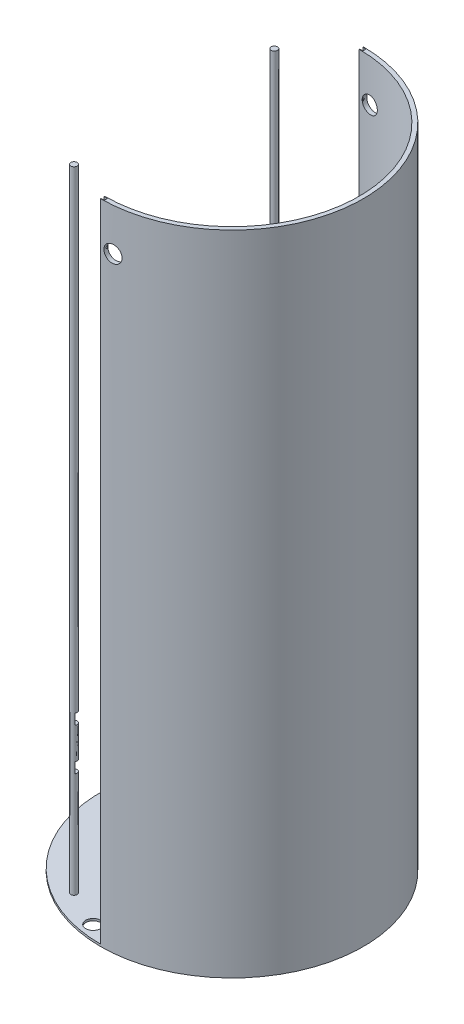
SolidWorks part; units mm, degrees
material "ABS"
ref_plane "Front Plane" through (0, 0, 0) normal (0, 0, 1) x (1, 0, 0)
ref_plane "Top Plane" through (0, 0, 0) normal (0, 1, 0) x (1, 0, 0)
ref_plane "Right Plane" through (0, 0, 0) normal (1, 0, 0) x (0, 0, -1)
sketch "Sketch2" plane through (0, 0, 0) normal (0, 1, 0) x (1, 0, 0)
  circle A0 centre (0, 0) radius 62.5
  circle A1 centre (0, 10) radius 0.75
  circle A2 centre (8.6603, -5) radius 0.75
  circle A3 centre (-8.6603, -5) radius 0.75
  point P12 (0, 0)
  dimension "D1" = 125
  dimension "D2" = 1.5
  dimension "D3" = 10
  dimension "D4" = 3
extrude "Boss-Extrude1" add sketch "Sketch2" along normal blind 1
sketch "Sketch3" plane through (0, 1, 0) normal (0, 1, 0) x (1, 0, 0)
  circle A0 centre (55, 0) radius 1.5
  dimension "D2" = 3
  dimension "D1" = 55
extrude "Boss-Extrude2" add sketch "Sketch3" along normal blind 300
ref_plane "Plane1" through (55, 0, 0) normal (1, 0, 0) x (0, 0, -1)
sketch "Sketch5" plane through (55, 0, 0) normal (1, 0, 0) x (0, 0, -1)
  line L0 (1.5, 1) -> (1.5, 301) construction
  line L1 (1.5, 56) -> (-1.5, 56)
  line L2 (1.5, 56) -> (1.5, 51)
  line L3 (1.5, 51) -> (-1.5, 51)
  line L4 (-1.5, 56) -> (-1.5, 51)
  line L5 (-1.5, 301) -> (-1.5, 1) construction
  line L6 (62.5, 1) -> (-62.5, 1) construction
  line L7 (1.5, 76) -> (1.5, 71)
  line L8 (1.5, 76) -> (-1.5, 76)
  line L9 (-1.5, 76) -> (-1.5, 71)
  line L10 (1.5, 71) -> (-1.5, 71)
  line L15 (1.5, 96) -> (1.5, 91) [skipped]
  line L16 (1.5, 96) -> (-1.5, 96) [skipped]
  line L17 (-1.5, 96) -> (-1.5, 91) [skipped]
  line L18 (1.5, 91) -> (-1.5, 91) [skipped]
  dimension "D1" = 5
  dimension "D2" = 50
  dimension "D3" = 3
extrude "Cut-Extrude1" cut sketch "Sketch5" against normal blind 5
pattern_circular "CirPattern1" count 3 over 360 about axis through (0, 0, 0) along (0, 1, 0) of "Boss-Extrude2", "Cut-Extrude1"
sketch "Sketch6" plane through (0, 1, 0) normal (0, 1, 0) x (1, 0, 0)
  line L0 (0, 0) -> (0, 62.5) construction
  line L2 (0, 0) -> (0, -62.5) construction
  line L3 (0, 62.5) -> (0, 60.5)
  line L4 (0, -60.5) -> (0, -62.5)
  arc A0 (0, -62.5) -> (0, 62.5) centre (0, 0) ccw
  circle A1 centre (0, 0) radius 62.5 construction
  arc A3 (0, 60.5) -> (0, -60.5) centre (0, 0) cw
  dimension "D2" = 2
  dimension "D1" = 180
  dimension "D3" = 2
extrude "Boss-Extrude3" add sketch "Sketch6" along normal blind 307 contours A0 L3 A3 L4
sketch "Sketch10" plane through (0, 308, 0) normal (0, 1, 0) x (1, 0, 0)
  line L0 (0, -60.5) -> (0, -62.5) construction
  line L1 (-1.5, -60.75) -> (1.5, -60.75)
  line L2 (-1.5, -60.75) -> (-1.5, -62.25)
  line L3 (-1.5, -62.25) -> (1.5, -62.25)
  line L4 (1.5, -60.75) -> (1.5, -62.25)
  line L5 (-1.5, -60.75) -> (1.5, -62.25) construction
  line L6 (-1.5, -62.25) -> (1.5, -60.75) construction
  line L8 (0, 62.5) -> (0, 60.5) construction
  line L9 (-1.5, 62.25) -> (1.5, 62.25)
  line L10 (-1.5, 62.25) -> (-1.5, 60.75)
  line L11 (-1.5, 60.75) -> (1.5, 60.75)
  line L12 (1.5, 62.25) -> (1.5, 60.75)
  line L13 (-1.5, 62.25) -> (1.5, 60.75) construction
  line L14 (-1.5, 60.75) -> (1.5, 62.25) construction
  point P0 (0, -61.5)
  point P9 (0, 61.5)
  line M9 (0, -60.5) -> (0, -62.5)
  dimension "D1" = 3
  dimension "D2" = 1.5
  dimension "D3" = 3
  dimension "D4" = 1.5
extrude "Cut-Extrude2" cut sketch "Sketch10" against normal up to next contours L4 L1 L3 M9 | L12 L11 L10 L9
sketch "Sketch11" plane through (0, 1, 0) normal (0, 1, 0) x (1, 0, 0)
  circle A0 centre (-57, 0) radius 3.5
  arc A3 (0, 62.5) -> (0, -62.5) centre (0, 0) ccw construction
  point P6 (-62.5, 0)
  dimension "D2" = 7
  dimension "D1" = 57
  dimension "D3" = 5.5
extrude "Cut-Extrude3" cut sketch "Sketch11" against normal blind 5
pattern_circular "CirPattern4" count 2 over 80 about axis through (0, 1, 0) along (0, 1, 0) of "Cut-Extrude3"
mirror "Mirror1" about plane through (0, 0, 0) normal (0, 0, 1) of "CirPattern4"
ref_plane "Plane3" through (0, 0, 62.5) normal (0, 0, 1) x (1, 0, 0)
sketch "Sketch15" plane through (0, 0, 62.5) normal (0, 0, 1) x (1, 0, 0)
  line L0 (62.5, 308) -> (0, 308) construction
  line L1 (0, 308) -> (0, 1) construction
  circle A0 centre (5, 288) radius 3.5
  dimension "D1" = 7
  dimension "D2" = 20
  dimension "D3" = 5
hole_wizard "CBORE for #6 Binding Head Machine Screw1" positions "3DSketch2" profile "Sketch16" counterbore size "#6" standard "ANSI Inch"
sketch3d "3DSketch2"
  point P0 (5.5612, 287.9317, 62.2521)
sketch "Sketch16" plane through (5.5612, 287.9317, 62.2521) normal (0, 1, 0) x (0.996, 0, -0.089)
  line L0 (0, 0) -> (0, 8.2934)
  line L1 (0, 8.2934) -> (2.1526, 7)
  line L2 (2.1526, 7) -> (2.1526, 2.2098)
  line L3 (2.1526, 2.2098) -> (3.9688, 2.2098)
  line L4 (3.9688, 2.2098) -> (3.9688, 0)
  line L5 (3.9688, 0) -> (0, 0)
  line L10 (0, 8.2934) -> (-2.1527, 7) construction
  line L11 (0, -6.35) -> (0, 107.95) construction
  dimension "Hole Dia." = 4.3053
  dimension "Hole Depth" = 7
  dimension "C'Bore Dia." = 7.9375
  dimension "C'Bore Depth" = 2.2098
  dimension "Drill Angle" = 118
mirror "Mirror3" about plane through (0, 0, 0) normal (0, 0, 1) of "CBORE for #6 Binding Head Machine Screw1"
